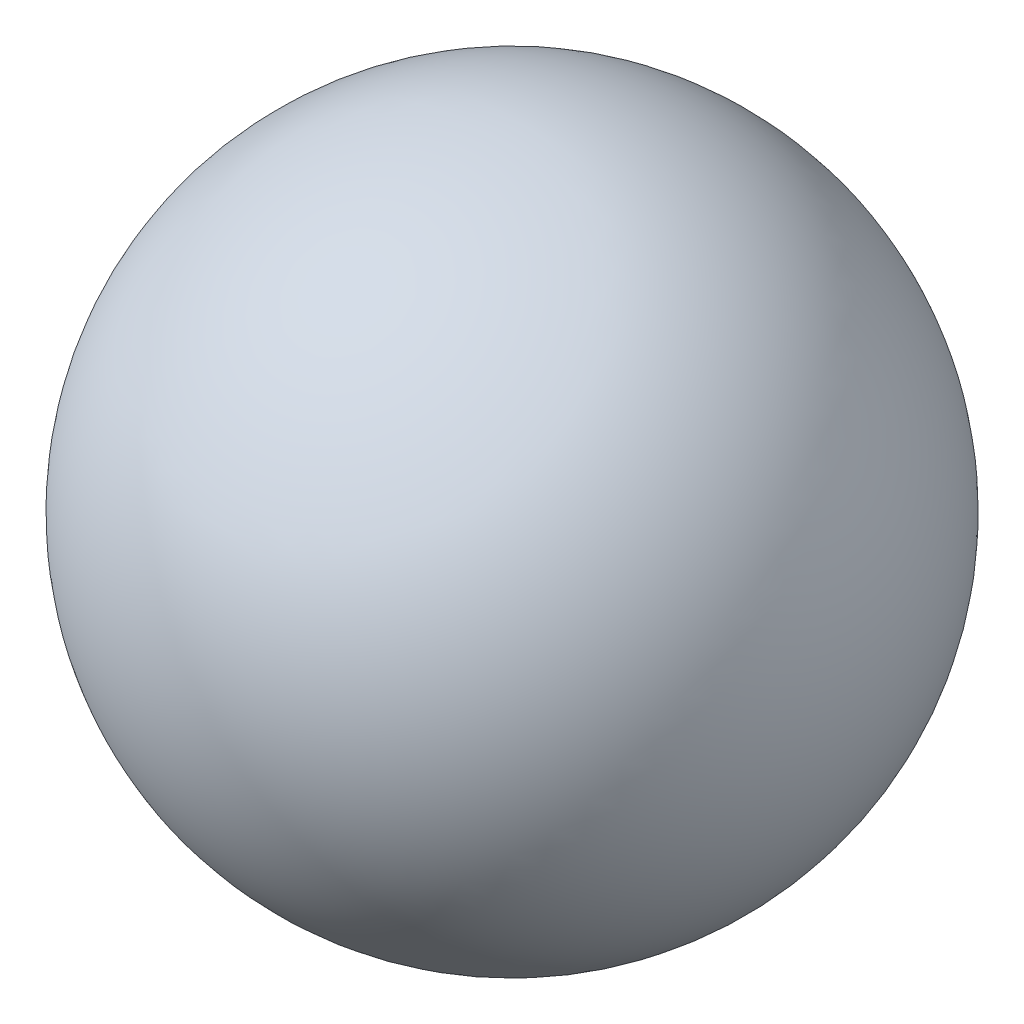
SolidWorks part; units mm, degrees
ref_plane "Front Plane" through (0, 0, 0) normal (0, 0, 1) x (1, 0, 0)
ref_plane "Top Plane" through (0, 0, 0) normal (0, 1, 0) x (1, 0, 0)
ref_plane "Right Plane" through (0, 0, 0) normal (1, 0, 0) x (0, 0, -1)
sketch "Sketch1" plane through (0, 0, 0) normal (0, 1, 0) x (1, 0, 0)
  line L0 (0, 0) -> (0, 40)
  arc A0 (0, 40) -> (0, 0) centre (0, 20) ccw
  dimension "D1" = 40
revolve "Revolve1" add sketch "Sketch1" angle 360 about L0
